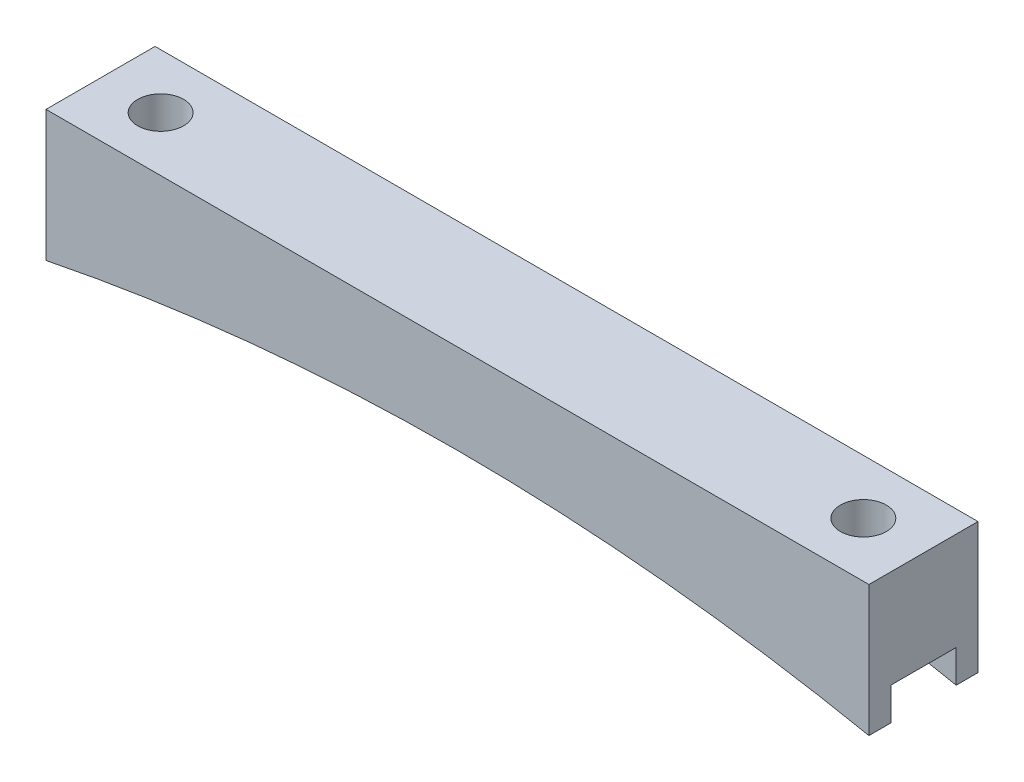
SolidWorks part; units mm, degrees
ref_plane "Front Plane" through (0, 0, 0) normal (0, 0, 1) x (1, 0, 0)
ref_plane "Top Plane" through (0, 0, 0) normal (0, 1, 0) x (1, 0, 0)
ref_plane "Right Plane" through (0, 0, 0) normal (1, 0, 0) x (0, 0, -1)
sketch "Sketch1" plane through (0, 0, 0) normal (0, 0, 1) x (1, 0, 0)
  line L0 (-47.915, 0) -> (47.915, 0)
  line L1 (-40.915, -2.54) -> (40.915, -2.54) construction
  line L2 (0, 0) -> (0, -4.6068) construction
  line L3 (47.915, 0) -> (47.915, -15.24)
  line L4 (-47.915, 0) -> (-47.915, -15.24)
  arc A0 (-47.915, -15.24) -> (47.915, -15.24) centre (0, -251.7349) cw
  point P4 (0, 0)
  point P9 (0, -2.54)
  dimension "D4" = 241.3
  dimension "D1" = 81.83
  dimension "D2" = 2.54
  dimension "D3" = 7
  dimension "D5" = 15.24
extrude "Boss-Extrude1" add sketch "Sketch1" along normal blind 12.7
sketch "Sketch2" plane through (0, 0, 0) normal (0, 1, 0) x (1, 0, 0)
  line L1 (-40.915, 0) -> (-40.915, -12.7) construction
  line L2 (-47.915, 0) -> (47.915, 0) construction
  line L3 (47.915, -12.7) -> (-47.915, -12.7) construction
  line L4 (40.915, 0) -> (40.915, -12.7) construction
  circle A0 centre (-40.915, -6.35) radius 2.675
  circle A1 centre (40.915, -6.35) radius 2.675
  circle A2 centre (-40.915, -6.35) radius 3 construction
  point P7 (-40.915, -6.35)
  dimension "D1" = 5.35
  dimension "D2" = 6
extrude "Cut-Extrude1" cut sketch "Sketch2" against normal through all
sketch "Sketch3" plane through (47.915, 0, 0) normal (1, 0, 0) x (0, 0, -1)
  line L0 (-12.7, -15.24) -> (0, -15.24) construction
  line L1 (-10.16, -15.24) -> (-2.54, -15.24)
  line L2 (-10.16, -15.24) -> (-10.16, -11.43)
  line L3 (-10.16, -11.43) -> (-2.54, -11.43)
  line L4 (-2.54, -15.24) -> (-2.54, -11.43)
  line L5 (-12.7, -15.24) -> (-12.7, 0) construction
  line L6 (0, -15.24) -> (0, 0) construction
  dimension "D1" = 2.54
  dimension "D2" = 2.54
  dimension "D3" = 3.81
extrude "Cut-Extrude2" cut sketch "Sketch3" against normal through all
